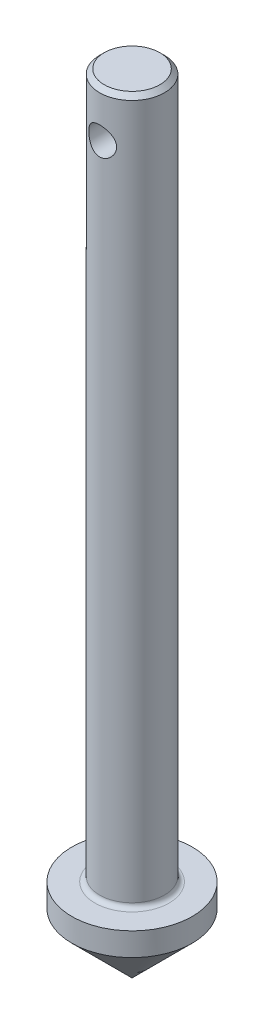
SolidWorks part; units mm, degrees
ref_plane "Płaszczyzna przednia" through (0, 0, 0) normal (0, 0, 1) x (1, 0, 0)
ref_plane "Płaszczyzna górna" through (0, 0, 0) normal (0, 1, 0) x (1, 0, 0)
ref_plane "Płaszczyzna prawa" through (0, 0, 0) normal (1, 0, 0) x (0, 0, -1)
sketch "Szkic1" plane through (0, 0, 0) normal (0, 0, 1) x (1, 0, 0)
  line L0 (0, 0) -> (0, 85) construction
  line L1 (0, 0) -> (6.5, 6.5)
  line L4 (6.5, 6.5) -> (6.5, 9)
  line L5 (6.5, 9) -> (4, 9)
  line L6 (3.5, 9.5) -> (3.5, 85)
  line L7 (3.5, 85) -> (0, 85)
  line L8 (0, 0) -> (0, 85)
  arc A0 (3.5, 9.5) -> (4, 9) centre (4, 9.5) ccw
  point P4 (0, 49.8605)
  point P7 (0, 84.6989)
  dimension "D4" = 3.5
  dimension "D5" = 0.5
  dimension "D1" = 6.5
  dimension "D2" = 85
  dimension "D3" = 2.5
  dimension "D6" = 76
  dimension "D7" = 45
revolve "Obrót2" add sketch "Szkic1" angle 360 about L0
sketch "Szkic2" plane through (0, 0, 0) normal (0, 0, 1) x (1, 0, 0)
  line L0 (3.5, 85) -> (-3.5, 85) construction
  line L1 (0, 85) -> (0, 80) construction
  circle A0 centre (0, 80) radius 1.5
  point P0 (0, 85)
  dimension "D2" = 3
  dimension "D1" = 5
extrude "Wytnij-wyciągnięcie1" cut sketch "Szkic2" against normal through all both and the other way through all
chamfer "Sfazowanie4" distance 0.5 angle 45 1 edges at (0, 85, -3.5)
